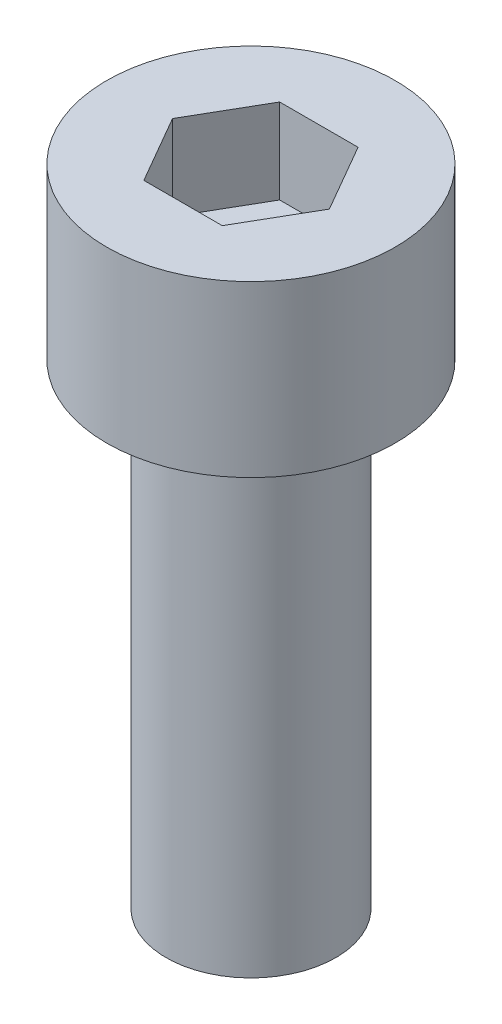
SolidWorks part; units mm, degrees
material "AISI 304"
ref_plane "前视基准面" through (0, 0, 0) normal (0, 0, 1) x (1, 0, 0)
ref_plane "上视基准面" through (0, 0, 0) normal (0, 1, 0) x (1, 0, 0)
ref_plane "右视基准面" through (0, 0, 0) normal (1, 0, 0) x (0, 0, -1)
sketch "草图1" plane through (0, 0, 0) normal (0, 1, 0) x (1, 0, 0)
  circle A0 centre (0, 0) radius 4.25
  dimension "D1" = 8.5
extrude "凸台-拉伸1" add sketch "草图1" along normal blind 5
sketch "草图2" plane through (0, 5, 0) normal (0, 1, 0) x (1, 0, 0)
  line L1 (2.3094, 0) -> (1.1547, 2)
  line L2 (1.1547, 2) -> (-1.1547, 2)
  line L3 (-1.1547, 2) -> (-2.3094, 0)
  line L4 (-2.3094, 0) -> (-1.1547, -2)
  line L5 (-1.1547, -2) -> (1.1547, -2)
  line L6 (1.1547, -2) -> (2.3094, 0)
  circle A0 centre (0, 0) radius 2 construction
  dimension "D1" = 4
extrude "切除-拉伸1" cut sketch "草图2" against normal blind 2.5
sketch "草图3" plane through (0, 0, 0) normal (0, -1, 0) x (1, 0, 0)
  circle A0 centre (0, 0) radius 2.5
  dimension "D1" = 5
extrude "凸台-拉伸2" add sketch "草图3" along normal blind 14
